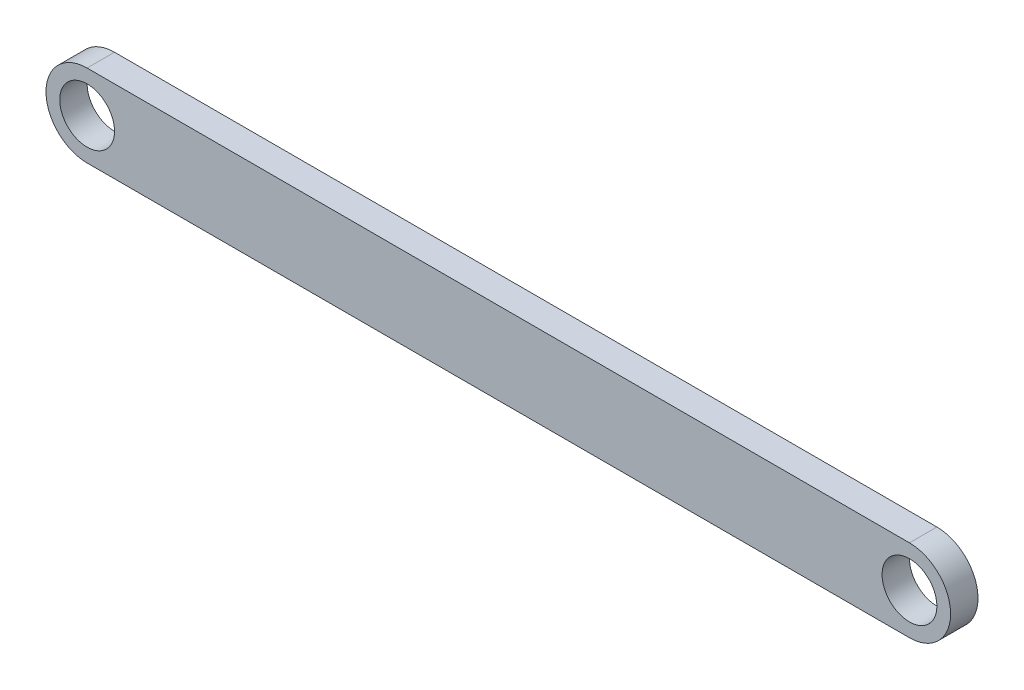
SolidWorks part; units mm, degrees
ref_plane "前视基准面" through (0, 0, 0) normal (0, 0, 1) x (1, 0, 0)
ref_plane "上视基准面" through (0, 0, 0) normal (0, 1, 0) x (1, 0, 0)
ref_plane "右视基准面" through (0, 0, 0) normal (1, 0, 0) x (0, 0, -1)
sketch "草图1" plane through (0, 0, 0) normal (0, 0, 1) x (1, 0, 0)
  line L1 (-44.7706, -3) -> (15.2294, -3)
  line L2 (-44.7706, 3) -> (15.2294, 3)
  arc A0 (15.2294, -3) -> (15.2294, 3) centre (15.2294, 0) ccw
  arc A1 (-44.7706, 3) -> (-44.7706, -3) centre (-44.7706, 0) ccw
  circle A2 centre (-44.7706, 0) radius 2
  circle A3 centre (15.2294, 0) radius 2
  dimension "D1" = 60
extrude "凸台-拉伸1" add sketch "草图1" along normal blind 2
